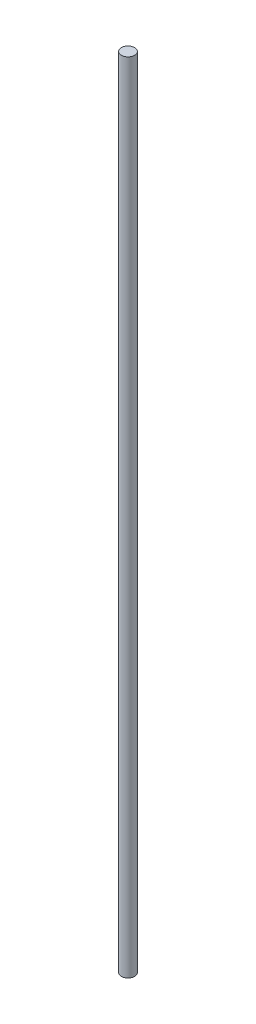
SolidWorks part; units mm, degrees
material "Hexcel AS4C (3000 Filaments)"
ref_plane "Front Plane" through (0, 0, 0) normal (0, 0, 1) x (1, 0, 0)
ref_plane "Top Plane" through (0, 0, 0) normal (0, 1, 0) x (1, 0, 0)
ref_plane "Right Plane" through (0, 0, 0) normal (1, 0, 0) x (0, 0, -1)
sketch "Sketch1" plane through (0, 0, 0) normal (0, 1, 0) x (1, 0, 0)
  circle A0 centre (0, 0) radius 2.5
  dimension "D1" = 5
extrude "Boss-Extrude1" add sketch "Sketch1" along normal blind 300
